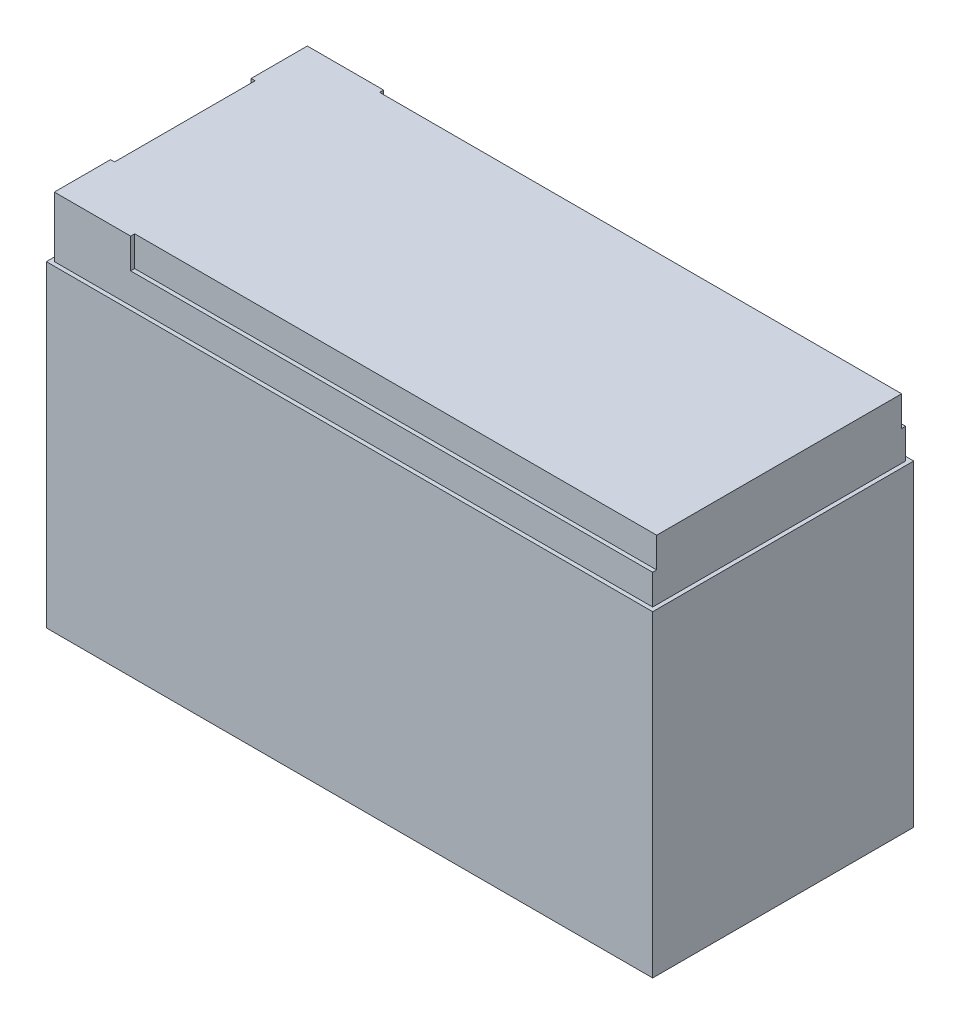
SolidWorks part; units mm, degrees
ref_plane "Front Plane" through (0, 0, 0) normal (0, 0, 1) x (1, 0, 0)
ref_plane "Top Plane" through (0, 0, 0) normal (0, 1, 0) x (1, 0, 0)
ref_plane "Right Plane" through (0, 0, 0) normal (1, 0, 0) x (0, 0, -1)
sketch "Sketch1" plane through (0, 0, 0) normal (0, 1, 0) x (1, 0, 0)
  line L1 (-75.5, -32.5) -> (75.5, -32.5)
  line L2 (-75.5, -32.5) -> (-75.5, 32.5)
  line L3 (-75.5, 32.5) -> (75.5, 32.5)
  line L4 (75.5, -32.5) -> (75.5, 32.5)
  line L5 (-75.5, -32.5) -> (75.5, 32.5) construction
  line L6 (-75.5, 32.5) -> (75.5, -32.5) construction
  point P0 (0, 0)
  dimension "D1" = 151
  dimension "D2" = 65
extrude "Boss-Extrude1" add sketch "Sketch1" along normal blind 94
sketch "Sketch2" plane through (0, 94, 0) normal (0, 1, 0) x (1, 0, 0)
  line L0 (-75.5, 32.5) -> (-75.5, -32.5) construction
  line L1 (-74.5, -31.5) -> (74.5, -31.5)
  line L2 (-74.5, -31.5) -> (-74.5, 31.5)
  line L3 (-74.5, 31.5) -> (74.5, 31.5)
  line L4 (74.5, -31.5) -> (74.5, 31.5)
  line L5 (-74.5, -31.5) -> (74.5, 31.5) construction
  line L6 (-74.5, 31.5) -> (74.5, -31.5) construction
  line L7 (-75.5, -32.5) -> (75.5, -32.5) construction
  line L8 (75.5, -32.5) -> (75.5, 32.5) construction
  line L9 (75.5, 32.5) -> (-75.5, 32.5) construction
  line L10 (75.5, -32.5) -> (75.5, 32.5)
  line L11 (-75.5, -32.5) -> (75.5, -32.5)
  line L12 (-75.5, 32.5) -> (-75.5, -32.5)
  line L13 (75.5, 32.5) -> (-75.5, 32.5)
  point P0 (0, 0)
  dimension "D1" = 1
  dimension "D2" = 1
extrude "Cut-Extrude1" cut sketch "Sketch2" against normal blind 15
sketch "Sketch3" plane through (0, 94, 0) normal (0, 1, 0) x (1, 0, 0)
  line L1 (74.5, 31.5) -> (-55.5, 31.5)
  line L2 (74.5, 31.5) -> (74.5, 30.5)
  line L3 (74.5, 30.5) -> (-55.5, 30.5)
  line L4 (-55.5, 31.5) -> (-55.5, 30.5)
  line L5 (74.5, -31.5) -> (-55.5, -31.5)
  line L6 (74.5, -31.5) -> (74.5, -30.5)
  line L7 (74.5, -30.5) -> (-55.5, -30.5)
  line L8 (-55.5, -31.5) -> (-55.5, -30.5)
  dimension "D1" = 1
  dimension "D2" = 1
  dimension "D3" = 130
  dimension "D4" = 130
extrude "Cut-Extrude2" cut sketch "Sketch3" against normal blind 7.5
sketch "Sketch4" plane through (0, 94, 0) normal (0, 1, 0) x (1, 0, 0)
  line L0 (-74.5, 31.5) -> (-74.5, -31.5) construction
  line L1 (-74.5, 17.5) -> (-73.5, 17.5)
  line L2 (-74.5, 17.5) -> (-74.5, -17.5)
  line L3 (-74.5, -17.5) -> (-73.5, -17.5)
  line L4 (-73.5, 17.5) -> (-73.5, -17.5)
  line L5 (-55.5, 31.5) -> (-74.5, 31.5) construction
  line L6 (-74.5, -31.5) -> (-55.5, -31.5) construction
  dimension "D1" = 1
  dimension "D2" = 14
  dimension "D3" = 14
extrude "Cut-Extrude3" cut sketch "Sketch4" against normal blind 7.5
